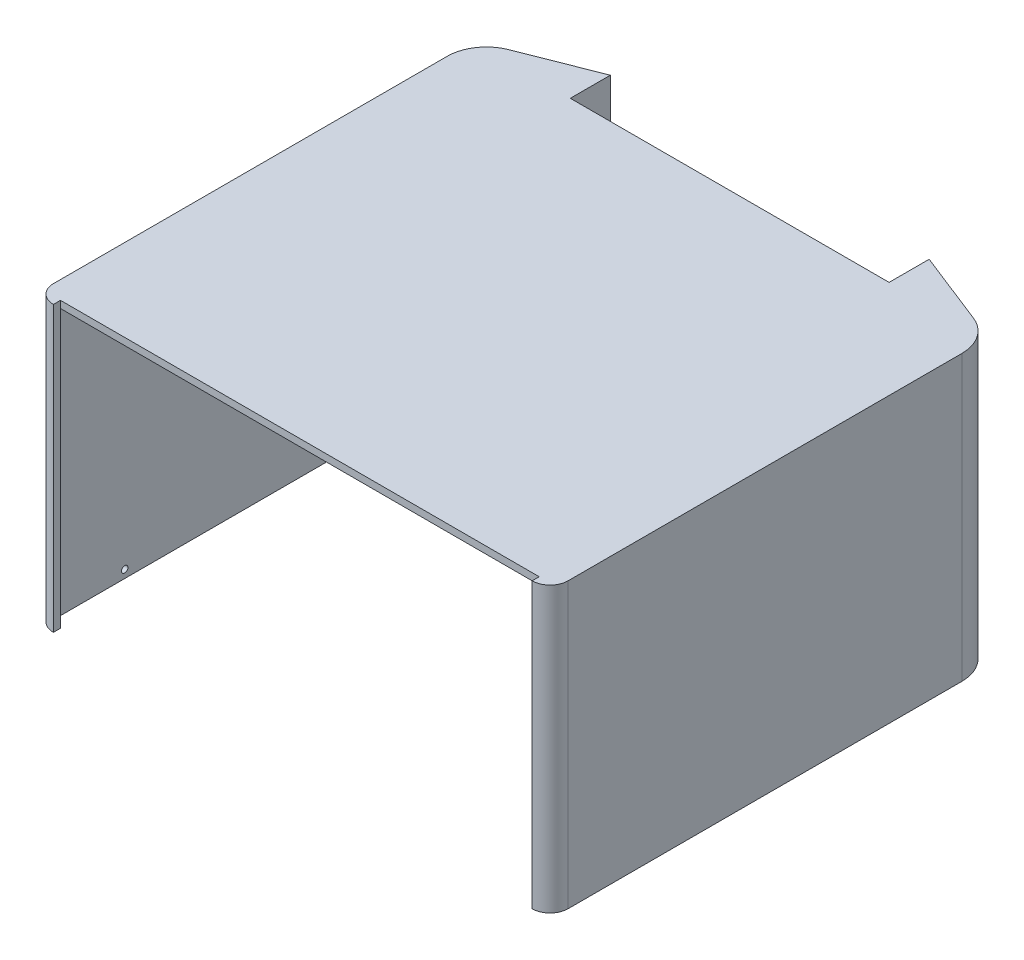
SolidWorks part; units mm, degrees
ref_plane "Front Plane" through (0, 0, 0) normal (0, 0, 1) x (1, 0, 0)
ref_plane "Top Plane" through (0, 0, 0) normal (0, 1, 0) x (1, 0, 0)
ref_plane "Right Plane" through (0, 0, 0) normal (1, 0, 0) x (0, 0, -1)
sketch "Sketch1" plane through (0, 0, 0) normal (0, 1, 0) x (1, 0, 0)
  line L0 (-49.6594, 72.6605) -> (48.7721, 72.6605)
  line L1 (-0.4437, -74.1395) -> (-0.4437, 72.6605)
  line L2 (-49.6594, 59.6605) -> (-50.0594, 59.6605) construction
  line L3 (-50.0594, 59.6605) -> (-49.6594, 59.6605) construction
  line L4 (-72.5188, 63.821) -> (-50.0594, 72.6605)
  line L5 (-79.7437, 53.213) -> (-79.7437, -3.8395)
  line L6 (49.1721, 59.6605) -> (48.7721, 59.6605) construction
  line L7 (48.7721, 59.6605) -> (49.1721, 59.6605) construction
  line L8 (-50.0594, 59.6605) -> (-50.0594, 71.156)
  line L9 (-78.3437, 53.213) -> (-78.3437, -3.8395)
  line L10 (50.5721, 59.6605) -> (50.5721, 70.605)
  line L11 (49.1721, 59.6605) -> (49.1721, 72.6605)
  line L12 (-78.3437, -3.8395) -> (-78.3437, -69.3395)
  line L13 (-74.9437, -72.7395) -> (74.0563, -72.7395)
  line L14 (49.1721, 59.6605) -> (50.5721, 59.6605)
  line L15 (78.8563, -3.8395) -> (78.8563, -69.3395)
  line L16 (71.1187, 62.5183) -> (50.5721, 70.605)
  line L17 (-72.006, 62.5183) -> (-51.4594, 70.605)
  line L18 (-79.7437, -3.8395) -> (-79.7437, -69.3395)
  line L19 (-74.9437, -74.1395) -> (74.0563, -74.1395)
  line L20 (77.4563, -3.8395) -> (77.4563, -69.3395)
  line L21 (77.4563, 53.213) -> (77.4563, -3.8395)
  line L22 (49.1721, 59.6605) -> (49.1721, 71.156)
  line L23 (-50.0594, 59.6605) -> (-51.4594, 59.6605)
  line L24 (-50.0594, 59.6605) -> (-50.0594, 72.6605)
  line L25 (-51.4594, 59.6605) -> (-51.4594, 70.605)
  line L26 (78.8563, 53.213) -> (78.8563, -3.8395)
  line L27 (71.6314, 63.821) -> (49.1721, 72.6605)
  arc A0 (78.8563, -69.3395) -> (74.0563, -74.1395) centre (74.0563, -69.3395) cw
  arc A1 (-78.3437, -69.3395) -> (-74.9437, -72.7395) centre (-74.9437, -69.3395) ccw
  arc A2 (78.8563, 53.213) -> (71.6314, 63.821) centre (67.4563, 53.213) ccw
  arc A3 (-78.3437, 53.213) -> (-72.006, 62.5183) centre (-68.3437, 53.213) cw
  arc A4 (77.4563, 53.213) -> (71.1187, 62.5183) centre (67.4563, 53.213) ccw
  arc A5 (-79.7437, 53.213) -> (-72.5188, 63.821) centre (-68.3437, 53.213) cw
  arc A6 (-79.7437, -69.3395) -> (-74.9437, -74.1395) centre (-74.9437, -69.3395) ccw
  arc A7 (77.4563, -69.3395) -> (74.0563, -72.7395) centre (74.0563, -69.3395) cw
  point P26 (-0.4437, -72.7395)
  dimension "D1" = 10
  dimension "D2" = 1.4
extrude "Boss-Extrude2" add sketch "Sketch1" along normal blind 82 contours L20 A7 L13 L1 L19 A0 L15 L26 A2 L27 L11 L14 L10 L16 A4 L21 | L18 A6 L19 L1 L13 A1 L12 L9 A3 L17 L25 L23 L8 L24 L4 A5 L5
sketch "Sketch3" plane through (0, 82, 0) normal (0, 1, 0) x (1, 0, 0)
  line L0 (-50.0594, 59.6605) -> (49.1721, 59.6605)
  line L16 (77.4563, 53.213) -> (77.4563, -69.3395)
  line L17 (74.0563, -72.7395) -> (-74.9437, -72.7395)
  line L18 (-78.3437, -69.3395) -> (-78.3437, 53.213)
  line L19 (-72.006, 62.5183) -> (-51.4594, 70.605)
  line L20 (-51.4594, 70.605) -> (-51.4594, 59.6605)
  line L21 (-51.4594, 59.6605) -> (-50.0594, 59.6605)
  line L22 (-50.0594, 59.6605) -> (-50.0594, 72.6605)
  line L23 (-50.0594, 72.6605) -> (-72.5188, 63.821)
  line L24 (-79.7437, 53.213) -> (-79.7437, -69.3395)
  line L25 (-74.9437, -74.1395) -> (74.0563, -74.1395)
  line L26 (78.8563, -69.3395) -> (78.8563, 53.213)
  line L27 (71.6314, 63.821) -> (49.1721, 72.6605)
  line L28 (49.1721, 72.6605) -> (49.1721, 59.6605)
  line L29 (49.1721, 59.6605) -> (50.5721, 59.6605)
  line L30 (50.5721, 59.6605) -> (50.5721, 70.605)
  line L31 (50.5721, 70.605) -> (71.1187, 62.5183)
  line L32 (77.4563, 53.213) -> (77.4563, -69.3395)
  line L33 (74.0563, -72.7395) -> (-74.9437, -72.7395)
  line L34 (-78.3437, -69.3395) -> (-78.3437, 53.213)
  line L35 (-72.006, 62.5183) -> (-51.4594, 70.605)
  line L36 (-51.4594, 70.605) -> (-51.4594, 59.6605)
  line L37 (-51.4594, 59.6605) -> (-50.0594, 59.6605)
  line L38 (-50.0594, 59.6605) -> (-50.0594, 72.6605)
  line L39 (-50.0594, 72.6605) -> (-72.5188, 63.821)
  line L40 (-79.7437, 53.213) -> (-79.7437, -69.3395)
  line L41 (-74.9437, -74.1395) -> (74.0563, -74.1395)
  line L42 (78.8563, -69.3395) -> (78.8563, 53.213)
  line L43 (71.6314, 63.821) -> (49.1721, 72.6605)
  line L44 (49.1721, 72.6605) -> (49.1721, 59.6605)
  line L45 (49.1721, 59.6605) -> (50.5721, 59.6605)
  line L46 (50.5721, 59.6605) -> (50.5721, 70.605)
  line L47 (50.5721, 70.605) -> (71.1187, 62.5183)
  arc A8 (74.0563, -72.7395) -> (77.4563, -69.3395) centre (74.0563, -69.3395) ccw
  arc A9 (-78.3437, -69.3395) -> (-74.9437, -72.7395) centre (-74.9437, -69.3395) ccw
  arc A10 (-72.006, 62.5183) -> (-78.3437, 53.213) centre (-68.3437, 53.213) ccw
  arc A11 (-72.5188, 63.821) -> (-79.7437, 53.213) centre (-68.3437, 53.213) ccw
  arc A12 (-79.7437, -69.3395) -> (-74.9437, -74.1395) centre (-74.9437, -69.3395) ccw
  arc A13 (74.0563, -74.1395) -> (78.8563, -69.3395) centre (74.0563, -69.3395) ccw
  arc A14 (78.8563, 53.213) -> (71.6314, 63.821) centre (67.4563, 53.213) ccw
  arc A15 (77.4563, 53.213) -> (71.1187, 62.5183) centre (67.4563, 53.213) ccw
  arc A16 (74.0563, -72.7395) -> (77.4563, -69.3395) centre (74.0563, -69.3395) ccw
  arc A17 (-78.3437, -69.3395) -> (-74.9437, -72.7395) centre (-74.9437, -69.3395) ccw
  arc A18 (-72.006, 62.5183) -> (-78.3437, 53.213) centre (-68.3437, 53.213) ccw
  arc A19 (-72.5188, 63.821) -> (-79.7437, 53.213) centre (-68.3437, 53.213) ccw
  arc A20 (-79.7437, -69.3395) -> (-74.9437, -74.1395) centre (-74.9437, -69.3395) ccw
  arc A21 (74.0563, -74.1395) -> (78.8563, -69.3395) centre (74.0563, -69.3395) ccw
  arc A22 (78.8563, 53.213) -> (71.6314, 63.821) centre (67.4563, 53.213) ccw
  arc A23 (77.4563, 53.213) -> (71.1187, 62.5183) centre (67.4563, 53.213) ccw
  line M25 (77.4563, 53.213) -> (77.4563, -69.3395)
  arc M26 (77.4563, -69.3395) -> (74.0563, -72.7395) centre (74.0563, -69.3395) cw
  line M27 (74.0563, -72.7395) -> (-74.9437, -72.7395)
  arc M28 (-74.9437, -72.7395) -> (-78.3437, -69.3395) centre (-74.9437, -69.3395) cw
  line M29 (-78.3437, -69.3395) -> (-78.3437, 53.213)
  arc M30 (-78.3437, 53.213) -> (-72.006, 62.5183) centre (-68.3437, 53.213) cw
  line M31 (-72.006, 62.5183) -> (-51.4594, 70.605)
  line M32 (-51.4594, 70.605) -> (-51.4594, 59.6605)
  line M33 (-51.4594, 59.6605) -> (-50.0594, 59.6605)
  line M45 (49.1721, 59.6605) -> (50.5721, 59.6605)
  line M46 (50.5721, 59.6605) -> (50.5721, 70.605)
  line M47 (50.5721, 70.605) -> (71.1187, 62.5183)
  arc M48 (71.1187, 62.5183) -> (77.4563, 53.213) centre (67.4563, 53.213) cw
  dimension "D1" = 0
extrude "Boss-Extrude3" add sketch "Sketch3" against normal blind 1.5 contours L0 M33 M32 M31 M30 M29 M28 M27 M26 M25 M48 M47 M46 M45
sketch "Sketch4" plane through (0, 0, 74.1395) normal (0, 0, 1) x (1, 0, 0)
  line L4 (-74.9437, 0) -> (74.0563, 0)
  line L5 (74.0563, 0) -> (74.0563, 82)
  line L6 (74.0563, 82) -> (-74.9437, 82)
  line L7 (-74.9437, 82) -> (-74.9437, 0)
  line L8 (-74.9437, 0) -> (74.0563, 0)
  line L9 (74.0563, 0) -> (74.0563, 82)
  line L10 (74.0563, 82) -> (-74.9437, 82)
  line L11 (-74.9437, 82) -> (-74.9437, 0)
  dimension "D1" = 0
extrude "Cut-Extrude2" cut sketch "Sketch4" against normal blind 1.5
sketch "Sketch5" plane through (0, 82, 0) normal (0, 1, 0) x (1, 0, 0)
  line L0 (-50.0594, 59.6605) -> (-50.0594, 59.4605)
  line L1 (-50.0594, 59.6605) -> (49.1721, 59.6605)
  line L2 (-50.0594, 59.4605) -> (49.1721, 59.4605)
  line L3 (49.1721, 59.6605) -> (49.1721, 59.4605)
  line L4 (49.1721, 59.6605) -> (49.1721, 72.6605) construction
  dimension "D1" = 0.2
extrude "Cut-Extrude3" cut sketch "Sketch5" against normal blind 18
sketch "Sketch6" plane through (-79.7437, 0, 0) normal (-1, 0, 0) x (0, 0, 1)
  line L1 (69.3395, 5) -> (49.3395, 5) construction
  line L2 (69.3395, 82) -> (69.3395, 0) construction
  line L3 (-53.213, 5) -> (-33.213, 5) construction
  line L4 (-53.213, 82) -> (-53.213, 0) construction
  line L5 (-53.213, 0) -> (69.3395, 0) construction
  line L6 (-33.213, 5) -> (-33.213, 0) construction
  line L7 (49.3395, 5) -> (49.3395, 0) construction
  circle A0 centre (-33.213, 2.5) radius 1
  circle A1 centre (49.3395, 2.5) radius 1
  dimension "D4" = 2
  dimension "D5" = 2
  dimension "D1" = 5
  dimension "D2" = 20
  dimension "D3" = 20
extrude "Cut-Extrude4" cut sketch "Sketch6" against normal blind 243
sketch "Sketch7" plane through (0, 80.5, 0) normal (0, -1, 0) x (1, 0, 0)
  line L14 (-50.0594, -59.4605) -> (49.1721, -59.4605)
  line L15 (49.1721, -59.4605) -> (49.1721, -59.6605)
  line L16 (49.1721, -59.6605) -> (50.5721, -59.6605)
  line L17 (50.5721, -59.6605) -> (50.5721, -70.605)
  line L18 (50.5721, -70.605) -> (71.1187, -62.5183)
  line L19 (77.4563, -53.213) -> (77.4563, 69.3395)
  line L20 (74.0563, 72.7395) -> (74.0563, 72.6395)
  line L21 (74.0563, 72.6395) -> (-74.9437, 72.6395)
  line L22 (-74.9437, 72.6395) -> (-74.9437, 72.7395)
  line L23 (-78.3437, 69.3395) -> (-78.3437, -53.213)
  line L24 (-72.006, -62.5183) -> (-51.4594, -70.605)
  line L25 (-51.4594, -70.605) -> (-51.4594, -59.6605)
  line L26 (-51.4594, -59.6605) -> (-50.0594, -59.6605)
  line L27 (-50.0594, -59.6605) -> (-50.0594, -59.4605)
  line L28 (-50.0594, -59.4605) -> (49.1721, -59.4605)
  line L29 (49.1721, -59.4605) -> (49.1721, -59.6605)
  line L30 (49.1721, -59.6605) -> (50.5721, -59.6605)
  line L31 (50.5721, -59.6605) -> (50.5721, -70.605)
  line L32 (50.5721, -70.605) -> (71.1187, -62.5183)
  line L33 (77.4563, -53.213) -> (77.4563, 69.3395)
  line L34 (74.0563, 72.7395) -> (74.0563, 72.6395)
  line L35 (74.0563, 72.6395) -> (-74.9437, 72.6395)
  line L36 (-74.9437, 72.6395) -> (-74.9437, 72.7395)
  line L37 (-78.3437, 69.3395) -> (-78.3437, -53.213)
  line L38 (-72.006, -62.5183) -> (-51.4594, -70.605)
  line L39 (-51.4594, -70.605) -> (-51.4594, -59.6605)
  line L40 (-51.4594, -59.6605) -> (-50.0594, -59.6605)
  line L41 (-50.0594, -59.6605) -> (-50.0594, -59.4605)
  arc A4 (71.1187, -62.5183) -> (77.4563, -53.213) centre (67.4563, -53.213) ccw
  arc A5 (77.4563, 69.3395) -> (74.0563, 72.7395) centre (74.0563, 69.3395) ccw
  arc A6 (-74.9437, 72.7395) -> (-78.3437, 69.3395) centre (-74.9437, 69.3395) ccw
  arc A7 (-78.3437, -53.213) -> (-72.006, -62.5183) centre (-68.3437, -53.213) ccw
  arc A8 (71.1187, -62.5183) -> (77.4563, -53.213) centre (67.4563, -53.213) ccw
  arc A9 (77.4563, 69.3395) -> (74.0563, 72.7395) centre (74.0563, 69.3395) ccw
  arc A10 (-74.9437, 72.7395) -> (-78.3437, 69.3395) centre (-74.9437, 69.3395) ccw
  arc A11 (-78.3437, -53.213) -> (-72.006, -62.5183) centre (-68.3437, -53.213) ccw
  dimension "D1" = 0
extrude "Cut-Extrude5" cut sketch "Sketch7" against normal blind 16.4
sketch "Sketch8" plane through (0, 82, 0) normal (0, 1, 0) x (1, 0, 0)
  line L0 (74.0563, -72.7395) -> (74.0563, -74.1395) construction
  line L1 (78.8563, -69.3395) -> (78.8563, 53.213) construction
  line L2 (71.6314, 63.821) -> (49.1721, 72.6605) construction
  line L3 (49.1721, 72.6605) -> (49.1721, 59.6605) construction
  line L4 (49.1721, 59.6605) -> (50.5721, 59.6605) construction
  line L5 (50.5721, 59.6605) -> (50.5721, 70.605) construction
  line L6 (50.5721, 70.605) -> (71.1187, 62.5183) construction
  line L7 (77.4563, 53.213) -> (77.4563, -69.3395) construction
  line L8 (-51.4594, 59.6605) -> (-50.0594, 59.6605) construction
  line L9 (-50.0594, 59.6605) -> (-50.0594, 72.6605) construction
  line L10 (-50.0594, 72.6605) -> (-72.5188, 63.821) construction
  line L11 (-79.7437, 53.213) -> (-79.7437, -69.3395) construction
  line L12 (-74.9437, -74.1395) -> (-74.9437, -72.7395) construction
  line L13 (-78.3437, -69.3395) -> (-78.3437, 53.213) construction
  line L14 (-72.006, 62.5183) -> (-51.4594, 70.605) construction
  line L15 (-51.4594, 70.605) -> (-51.4594, 59.6605) construction
  line L16 (74.0563, -72.7395) -> (74.0563, -74.1395)
  line L17 (78.8563, -69.3395) -> (78.8563, 53.213)
  line L18 (71.6314, 63.821) -> (49.1721, 72.6605)
  line L19 (49.1721, 72.6605) -> (49.1721, 59.6605)
  line L20 (49.1721, 59.6605) -> (50.5721, 59.6605)
  line L21 (50.5721, 59.6605) -> (50.5721, 70.605)
  line L22 (50.5721, 70.605) -> (71.1187, 62.5183)
  line L23 (77.4563, 53.213) -> (77.4563, -69.3395)
  line L24 (-51.4594, 59.6605) -> (-50.0594, 59.6605)
  line L25 (-50.0594, 59.6605) -> (-50.0594, 72.6605)
  line L26 (-50.0594, 72.6605) -> (-72.5188, 63.821)
  line L27 (-79.7437, 53.213) -> (-79.7437, -69.3395)
  line L28 (-74.9437, -74.1395) -> (-74.9437, -72.7395)
  line L29 (-78.3437, -69.3395) -> (-78.3437, 53.213)
  line L30 (-72.006, 62.5183) -> (-51.4594, 70.605)
  line L31 (-51.4594, 70.605) -> (-51.4594, 59.6605)
  arc A0 (74.0563, -72.7395) -> (77.4563, -69.3395) centre (74.0563, -69.3395) ccw construction
  arc A1 (74.0563, -74.1395) -> (78.8563, -69.3395) centre (74.0563, -69.3395) ccw construction
  arc A2 (78.8563, 53.213) -> (71.6314, 63.821) centre (67.4563, 53.213) ccw construction
  arc A3 (77.4563, 53.213) -> (71.1187, 62.5183) centre (67.4563, 53.213) ccw construction
  arc A4 (-72.5188, 63.821) -> (-79.7437, 53.213) centre (-68.3437, 53.213) ccw construction
  arc A5 (-79.7437, -69.3395) -> (-74.9437, -74.1395) centre (-74.9437, -69.3395) ccw construction
  arc A6 (-78.3437, -69.3395) -> (-74.9437, -72.7395) centre (-74.9437, -69.3395) ccw construction
  arc A7 (-72.006, 62.5183) -> (-78.3437, 53.213) centre (-68.3437, 53.213) ccw construction
  arc A8 (74.0563, -72.7395) -> (77.4563, -69.3395) centre (74.0563, -69.3395) ccw
  arc A9 (74.0563, -74.1395) -> (78.8563, -69.3395) centre (74.0563, -69.3395) ccw
  arc A10 (78.8563, 53.213) -> (71.6314, 63.821) centre (67.4563, 53.213) ccw
  arc A11 (77.4563, 53.213) -> (71.1187, 62.5183) centre (67.4563, 53.213) ccw
  arc A12 (-72.5188, 63.821) -> (-79.7437, 53.213) centre (-68.3437, 53.213) ccw
  arc A13 (-79.7437, -69.3395) -> (-74.9437, -74.1395) centre (-74.9437, -69.3395) ccw
  arc A14 (-78.3437, -69.3395) -> (-74.9437, -72.7395) centre (-74.9437, -69.3395) ccw
  arc A15 (-72.006, 62.5183) -> (-78.3437, 53.213) centre (-68.3437, 53.213) ccw
extrude "Boss-Extrude4" add sketch "Sketch8" along normal blind 5
sketch "Sketch9" plane through (0, 87, 0) normal (0, 1, 0) x (1, 0, 0)
  line L0 (74.0563, -72.7395) -> (74.0563, -74.1395) construction
  line L1 (78.8563, -69.3395) -> (78.8563, 53.213) construction
  line L2 (71.6314, 63.821) -> (49.1721, 72.6605) construction
  line L3 (49.1721, 72.6605) -> (49.1721, 59.6605) construction
  line L4 (49.1721, 59.6605) -> (50.5721, 59.6605) construction
  line L5 (50.5721, 59.6605) -> (50.5721, 70.605) construction
  line L6 (50.5721, 70.605) -> (71.1187, 62.5183) construction
  line L7 (77.4563, 53.213) -> (77.4563, -69.3395) construction
  line L8 (-51.4594, 70.605) -> (-51.4594, 59.6605) construction
  line L9 (-51.4594, 59.6605) -> (-50.0594, 59.6605) construction
  line L10 (-50.0594, 59.6605) -> (-50.0594, 72.6605) construction
  line L11 (-50.0594, 72.6605) -> (-72.5188, 63.821) construction
  line L12 (-79.7437, 53.213) -> (-79.7437, -69.3395) construction
  line L13 (-74.9437, -74.1395) -> (-74.9437, -72.7395) construction
  line L14 (-78.3437, -69.3395) -> (-78.3437, 53.213) construction
  line L15 (-72.006, 62.5183) -> (-51.4594, 70.605) construction
  line L16 (74.0563, -72.7395) -> (74.0563, -74.1395)
  line L17 (78.8563, -69.3395) -> (78.8563, 53.213)
  line L18 (71.6314, 63.821) -> (49.1721, 72.6605)
  line L19 (49.1721, 72.6605) -> (49.1721, 59.6605)
  line L20 (49.1721, 59.6605) -> (50.5721, 59.6605)
  line L21 (50.5721, 59.6605) -> (50.5721, 70.605)
  line L22 (50.5721, 70.605) -> (71.1187, 62.5183)
  line L23 (77.4563, 53.213) -> (77.4563, -69.3395)
  line L24 (-51.4594, 70.605) -> (-51.4594, 59.6605)
  line L25 (-51.4594, 59.6605) -> (-50.0594, 59.6605)
  line L26 (-50.0594, 59.6605) -> (-50.0594, 72.6605)
  line L27 (-50.0594, 72.6605) -> (-72.5188, 63.821)
  line L28 (-79.7437, 53.213) -> (-79.7437, -69.3395)
  line L29 (-74.9437, -74.1395) -> (-74.9437, -72.7395)
  line L30 (-78.3437, -69.3395) -> (-78.3437, 53.213)
  line L31 (-72.006, 62.5183) -> (-51.4594, 70.605)
  line L32 (-50.0594, 59.6605) -> (49.1721, 59.6605)
  line L33 (74.0563, -72.7395) -> (-74.9437, -72.7395)
  arc A0 (74.0563, -72.7395) -> (77.4563, -69.3395) centre (74.0563, -69.3395) ccw construction
  arc A1 (74.0563, -74.1395) -> (78.8563, -69.3395) centre (74.0563, -69.3395) ccw construction
  arc A2 (78.8563, 53.213) -> (71.6314, 63.821) centre (67.4563, 53.213) ccw construction
  arc A3 (77.4563, 53.213) -> (71.1187, 62.5183) centre (67.4563, 53.213) ccw construction
  arc A4 (-72.5188, 63.821) -> (-79.7437, 53.213) centre (-68.3437, 53.213) ccw construction
  arc A5 (-79.7437, -69.3395) -> (-74.9437, -74.1395) centre (-74.9437, -69.3395) ccw construction
  arc A6 (-78.3437, -69.3395) -> (-74.9437, -72.7395) centre (-74.9437, -69.3395) ccw construction
  arc A7 (-72.006, 62.5183) -> (-78.3437, 53.213) centre (-68.3437, 53.213) ccw construction
  arc A8 (74.0563, -72.7395) -> (77.4563, -69.3395) centre (74.0563, -69.3395) ccw
  arc A9 (74.0563, -74.1395) -> (78.8563, -69.3395) centre (74.0563, -69.3395) ccw
  arc A10 (78.8563, 53.213) -> (71.6314, 63.821) centre (67.4563, 53.213) ccw
  arc A11 (77.4563, 53.213) -> (71.1187, 62.5183) centre (67.4563, 53.213) ccw
  arc A12 (-72.5188, 63.821) -> (-79.7437, 53.213) centre (-68.3437, 53.213) ccw
  arc A13 (-79.7437, -69.3395) -> (-74.9437, -74.1395) centre (-74.9437, -69.3395) ccw
  arc A14 (-78.3437, -69.3395) -> (-74.9437, -72.7395) centre (-74.9437, -69.3395) ccw
  arc A15 (-72.006, 62.5183) -> (-78.3437, 53.213) centre (-68.3437, 53.213) ccw
  line M1 (-51.4594, 70.605) -> (-51.4594, 59.6605)
  line M2 (-51.4594, 59.6605) -> (-50.0594, 59.6605)
  line M3 (-50.0594, 59.6605) -> (-50.0594, 72.6605)
  line M4 (-50.0594, 72.6605) -> (-72.5188, 63.821)
  arc M5 (-72.5188, 63.821) -> (-79.7437, 53.213) centre (-68.3437, 53.213) ccw
  line M6 (-79.7437, 53.213) -> (-79.7437, -69.3395)
  arc M7 (-79.7437, -69.3395) -> (-74.9437, -74.1395) centre (-74.9437, -69.3395) ccw
  line M8 (-74.9437, -74.1395) -> (-74.9437, -72.7395)
  arc M9 (-74.9437, -72.7395) -> (-78.3437, -69.3395) centre (-74.9437, -69.3395) cw
  line M10 (-78.3437, -69.3395) -> (-78.3437, 53.213)
  arc M11 (-78.3437, 53.213) -> (-72.006, 62.5183) centre (-68.3437, 53.213) cw
  line M12 (-72.006, 62.5183) -> (-51.4594, 70.605)
extrude "Boss-Extrude6" add sketch "Sketch9" along normal blind 1.4 contours L23 A11 L22 L21 L20 L32 L33 A8 M2 M1 M12 M11 M10 M9 | M12 M1 M2 M3 M4 M5 M6 M7 M8 M9 M10 M11 | A11 L23 A8 L16 A9 L17 A10 L18 L19 L20 L21 L22
sketch "Sketch10" plane through (0, 0, -59.6605) normal (0, 0, -1) x (-1, 0, 0)
  line L0 (-49.1721, 88.4) -> (-49.1721, 81.66)
  line L1 (-49.1721, 88.4) -> (50.0594, 88.4)
  line L2 (-49.1721, 81.66) -> (50.0594, 81.66)
  line L3 (50.0594, 88.4) -> (50.0594, 81.66)
  line L4 (-49.1721, 87) -> (50.0594, 87)
  line L5 (50.0594, 87) -> (50.0594, 88.4)
  line L6 (50.0594, 88.4) -> (-49.1721, 88.4)
  line L7 (-49.1721, 88.4) -> (-49.1721, 87)
  line L8 (-49.1721, 87) -> (50.0594, 87)
  line L9 (50.0594, 87) -> (50.0594, 88.4)
  line L10 (50.0594, 88.4) -> (-49.1721, 88.4)
  line L11 (-49.1721, 88.4) -> (-49.1721, 87)
  line L12 (-49.1721, 88.4) -> (-49.1721, 0) construction
  line M7 (-49.1721, 87) -> (50.0594, 87)
  line M8 (50.0594, 87) -> (50.0594, 88.4)
  line M9 (50.0594, 88.4) -> (-49.1721, 88.4)
  line M10 (-49.1721, 88.4) -> (-49.1721, 87)
  dimension "D2" = 6.74
  dimension "D1" = 0
extrude "Boss-Extrude7" add sketch "Sketch10" along normal blind 1.4 contours L3 L0 L2 M7 | M10 M7 M8 M9
sketch "Sketch11" plane through (0, 88.4, 0) normal (0, 1, 0) x (1, 0, 0)
  line L0 (48.3721, 61.8605) -> (-49.2594, 61.8605)
  line L1 (-49.2594, 61.8605) -> (-49.2594, 73.8351)
  line L2 (-49.2594, 73.8351) -> (-72.8117, 64.5654)
  line L3 (-80.5437, 53.213) -> (-80.5437, -69.3395)
  line L4 (-74.1437, -74.882) -> (-74.1437, -73.5395)
  line L5 (-74.1437, -73.5395) -> (73.2563, -73.5395)
  line L6 (73.2563, -73.5395) -> (73.2563, -74.882)
  line L7 (79.6563, -69.3395) -> (79.6563, 53.213)
  line L8 (71.9244, 64.5654) -> (48.3721, 73.8351)
  line L9 (48.3721, 73.8351) -> (48.3721, 61.8605)
  line L10 (49.1721, 61.0605) -> (-50.0594, 61.0605)
  line L11 (-50.0594, 61.0605) -> (-50.0594, 72.6605)
  line L12 (-50.0594, 72.6605) -> (-72.5188, 63.821)
  line L13 (-79.7437, 53.213) -> (-79.7437, -69.3395)
  line L14 (-74.9437, -74.1395) -> (-74.9437, -72.7395)
  line L15 (-74.9437, -72.7395) -> (74.0563, -72.7395)
  line L16 (74.0563, -72.7395) -> (74.0563, -74.1395)
  line L17 (78.8563, -69.3395) -> (78.8563, 53.213)
  line L18 (71.6314, 63.821) -> (49.1721, 72.6605)
  line L19 (49.1721, 72.6605) -> (49.1721, 61.0605)
  line L20 (49.1721, 61.0605) -> (-50.0594, 61.0605)
  line L21 (-50.0594, 61.0605) -> (-50.0594, 72.6605)
  line L22 (-50.0594, 72.6605) -> (-72.5188, 63.821)
  line L23 (-79.7437, 53.213) -> (-79.7437, -69.3395)
  line L24 (-74.9437, -74.1395) -> (-74.9437, -72.7395)
  line L25 (-74.9437, -72.7395) -> (74.0563, -72.7395)
  line L26 (74.0563, -72.7395) -> (74.0563, -74.1395)
  line L27 (78.8563, -69.3395) -> (78.8563, 53.213)
  line L28 (71.6314, 63.821) -> (49.1721, 72.6605)
  line L29 (49.1721, 72.6605) -> (49.1721, 61.0605)
  line L30 (-50.0594, 68.9712) -> (-50.0594, 78.2374)
  line L31 (49.1721, 70.3918) -> (49.1721, 77.7926)
  line L32 (74.0563, -72.7395) -> (74.0563, -77.4077)
  line L33 (-74.9437, -72.7395) -> (-74.9437, -78.4457)
  arc A0 (-72.8117, 64.5654) -> (-80.5437, 53.213) centre (-68.3437, 53.213) ccw
  arc A1 (-80.5437, -69.3395) -> (-74.1437, -74.882) centre (-74.9437, -69.3395) ccw
  arc A2 (73.2563, -74.882) -> (79.6563, -69.3395) centre (74.0563, -69.3395) ccw
  arc A3 (79.6563, 53.213) -> (71.9244, 64.5654) centre (67.4563, 53.213) ccw
  arc A4 (-72.5188, 63.821) -> (-79.7437, 53.213) centre (-68.3437, 53.213) ccw
  arc A5 (-79.7437, -69.3395) -> (-74.9437, -74.1395) centre (-74.9437, -69.3395) ccw
  arc A6 (74.0563, -74.1395) -> (78.8563, -69.3395) centre (74.0563, -69.3395) ccw
  arc A7 (78.8563, 53.213) -> (71.6314, 63.821) centre (67.4563, 53.213) ccw
  arc A8 (-72.5188, 63.821) -> (-79.7437, 53.213) centre (-68.3437, 53.213) ccw
  arc A9 (-79.7437, -69.3395) -> (-74.9437, -74.1395) centre (-74.9437, -69.3395) ccw
  arc A10 (74.0563, -74.1395) -> (78.8563, -69.3395) centre (74.0563, -69.3395) ccw
  arc A11 (78.8563, 53.213) -> (71.6314, 63.821) centre (67.4563, 53.213) ccw
  line M17 (-50.0594, 72.6605) -> (-72.5188, 63.821)
  arc M18 (-72.5188, 63.821) -> (-79.7437, 53.213) centre (-68.3437, 53.213) ccw
  line M19 (-79.7437, 53.213) -> (-79.7437, -69.3395)
  arc M20 (-79.7437, -69.3395) -> (-74.9437, -74.1395) centre (-74.9437, -69.3395) ccw
  arc M24 (74.0563, -74.1395) -> (78.8563, -69.3395) centre (74.0563, -69.3395) ccw
  line M25 (78.8563, -69.3395) -> (78.8563, 53.213)
  arc M26 (78.8563, 53.213) -> (71.6314, 63.821) centre (67.4563, 53.213) ccw
  line M27 (71.6314, 63.821) -> (49.1721, 72.6605)
  dimension "D1" = 0
  dimension "D2" = 0.8
extrude "Boss-Extrude8" add sketch "Sketch11" against normal up to surface (88.4 mm away) contours L7 A3 L8 L31 L32 A2 M27 M26 M25 M24 | L3 A1 L33 L30 L2 A0 M20 M19 M18 M17 up to face at (67.3119, 0, -17.5155)
sketch "Sketch12" plane through (0, 87, 0) normal (0, -1, 0) x (1, 0, 0)
  line L8 (-51.4594, -59.6605) -> (50.5721, -59.6605)
  line L9 (50.5721, -59.6605) -> (50.5721, -70.605)
  line L10 (50.5721, -70.605) -> (71.1187, -62.5183)
  line L11 (77.4563, -53.213) -> (77.4563, 69.3395)
  line L12 (74.0563, 72.7395) -> (-74.9437, 72.7395)
  line L13 (-78.3437, 69.3395) -> (-78.3437, -53.213)
  line L14 (-72.006, -62.5183) -> (-51.4594, -70.605)
  line L15 (-51.4594, -70.605) -> (-51.4594, -59.6605)
  line L16 (-51.4594, -59.6605) -> (50.5721, -59.6605)
  line L17 (50.5721, -59.6605) -> (50.5721, -70.605)
  line L18 (50.5721, -70.605) -> (71.1187, -62.5183)
  line L19 (77.4563, -53.213) -> (77.4563, 69.3395)
  line L20 (74.0563, 72.7395) -> (-74.9437, 72.7395)
  line L21 (-78.3437, 69.3395) -> (-78.3437, -53.213)
  line L22 (-72.006, -62.5183) -> (-51.4594, -70.605)
  line L23 (-51.4594, -70.605) -> (-51.4594, -59.6605)
  arc A4 (71.1187, -62.5183) -> (77.4563, -53.213) centre (67.4563, -53.213) ccw
  arc A5 (77.4563, 69.3395) -> (74.0563, 72.7395) centre (74.0563, 69.3395) ccw
  arc A6 (-74.9437, 72.7395) -> (-78.3437, 69.3395) centre (-74.9437, 69.3395) ccw
  arc A7 (-78.3437, -53.213) -> (-72.006, -62.5183) centre (-68.3437, -53.213) ccw
  arc A8 (71.1187, -62.5183) -> (77.4563, -53.213) centre (67.4563, -53.213) ccw
  arc A9 (77.4563, 69.3395) -> (74.0563, 72.7395) centre (74.0563, 69.3395) ccw
  arc A10 (-74.9437, 72.7395) -> (-78.3437, 69.3395) centre (-74.9437, 69.3395) ccw
  arc A11 (-78.3437, -53.213) -> (-72.006, -62.5183) centre (-68.3437, -53.213) ccw
  dimension "D1" = 0
extrude "Boss-Extrude9" add sketch "Sketch12" along normal blind 0.8
sketch "Sketch13" plane through (-51.4594, 0, 0) normal (-1, 0, 0) x (0, 0, 1)
  line L4 (-59.6605, 86.2) -> (-70.605, 86.2)
  line L5 (-70.605, 86.2) -> (-70.605, 0)
  line L6 (-70.605, 0) -> (-59.6605, 0)
  line L7 (-59.6605, 0) -> (-59.6605, 86.2)
  line L8 (-59.6605, 86.2) -> (-70.605, 86.2)
  line L9 (-70.605, 86.2) -> (-70.605, 0)
  line L10 (-70.605, 0) -> (-59.6605, 0)
  line L11 (-59.6605, 0) -> (-59.6605, 86.2)
  dimension "D1" = 0
extrude "Boss-Extrude10" add sketch "Sketch13" along normal blind 0.8
